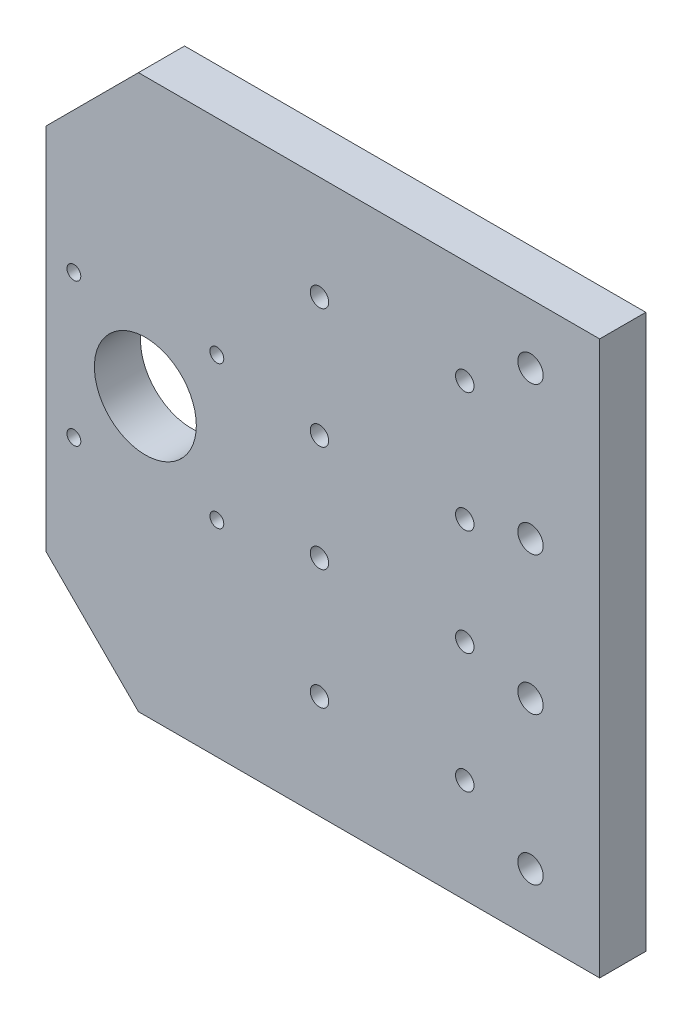
SolidWorks part; units mm, degrees
ref_plane "Ön Düzlem" through (0, 0, 0) normal (0, 0, 1) x (1, 0, 0)
ref_plane "Üst Düzlem" through (0, 0, 0) normal (0, 1, 0) x (1, 0, 0)
ref_plane "Sağ Düzlem" through (0, 0, 0) normal (1, 0, 0) x (0, 0, -1)
sketch "Sketch1" plane through (0, 0, 0) normal (0, 0, 1) x (1, 0, 0)
  line L0 (0, -60) -> (0, 60)
  line L1 (0, 60) -> (-100, 60)
  line L2 (-120, 40) -> (-120, -40)
  line L3 (-100, -60) -> (0, -60)
  line L4 (-45, 24.5) -> (-45, -24.5) construction
  line L5 (-114, -15.5) -> (-83, -15.5) construction
  line L6 (-114, -15.5) -> (-114, 15.5) construction
  line L7 (-114, 15.5) -> (-83, 15.5) construction
  line L8 (-83, -15.5) -> (-83, 15.5) construction
  line L9 (-114, -15.5) -> (-83, 15.5) construction
  line L10 (-114, 15.5) -> (-83, -15.5) construction
  line L11 (-60.75, 11.5) -> (-29.25, 11.5) construction
  line L12 (-60.75, 11.5) -> (-60.75, 37.5) construction
  line L13 (-60.75, 37.5) -> (-29.25, 37.5) construction
  line L14 (-29.25, 11.5) -> (-29.25, 37.5) construction
  line L15 (-60.75, 11.5) -> (-29.25, 37.5) construction
  line L16 (-60.75, 37.5) -> (-29.25, 11.5) construction
  line L17 (-60.75, -37.5) -> (-29.25, -37.5) construction
  line L18 (-60.75, -37.5) -> (-60.75, -11.5) construction
  line L19 (-60.75, -11.5) -> (-29.25, -11.5) construction
  line L20 (-29.25, -37.5) -> (-29.25, -11.5) construction
  line L21 (-60.75, -37.5) -> (-29.25, -11.5) construction
  line L22 (-60.75, -11.5) -> (-29.25, -37.5) construction
  line L23 (-100, 60) -> (-120, 40)
  line L24 (-120, -40) -> (-100, -60)
  line L25 (-15, 47) -> (-15, 15) construction
  line L26 (-15, -15) -> (-15, -47) construction
  line L27 (-15, 31) -> (-15, -31) construction
  circle A0 centre (-98.5, 0) radius 11.05
  circle A1 centre (-83, 15.5) radius 1.5
  circle A2 centre (-114, 15.5) radius 1.5
  circle A3 centre (-114, -15.5) radius 1.5
  circle A4 centre (-83, -15.5) radius 1.5
  circle A5 centre (-60.75, 37.5) radius 2
  circle A6 centre (-29.25, 37.5) radius 2
  circle A7 centre (-60.75, 11.5) radius 2
  circle A8 centre (-29.25, 11.5) radius 2
  circle A9 centre (-60.75, -11.5) radius 2
  circle A10 centre (-29.25, -11.5) radius 2
  circle A11 centre (-29.25, -37.5) radius 2
  circle A12 centre (-60.75, -37.5) radius 2
  circle A13 centre (-15, 47) radius 2.75
  circle A14 centre (-15, 15) radius 2.75
  circle A15 centre (-15, -15) radius 2.75
  circle A16 centre (-15, -47) radius 2.75
  point P0 (-120, -60)
  point P4 (0, 0)
  point P6 (-120, 60)
  point P16 (-45, -24.5)
  point P19 (-45, 24.5)
  point P29 (-45, 0)
  point P51 (-15, 0)
  dimension "D3" = 22.1
  dimension "D5" = 3
  dimension "D6" = 6
  dimension "D11" = 4
  dimension "D13" = 5.5
  dimension "D16" = 15
  dimension "D1" = 120
  dimension "D2" = 120
  dimension "D4" = 31
  dimension "D7" = 31.5
  dimension "D8" = 26
  dimension "D9" = 23
  dimension "D10" = 45
  dimension "D12" = 32
  dimension "D17" = 30
extrude "Boss-Extrude1" add sketch "Sketch1" along normal blind 10
